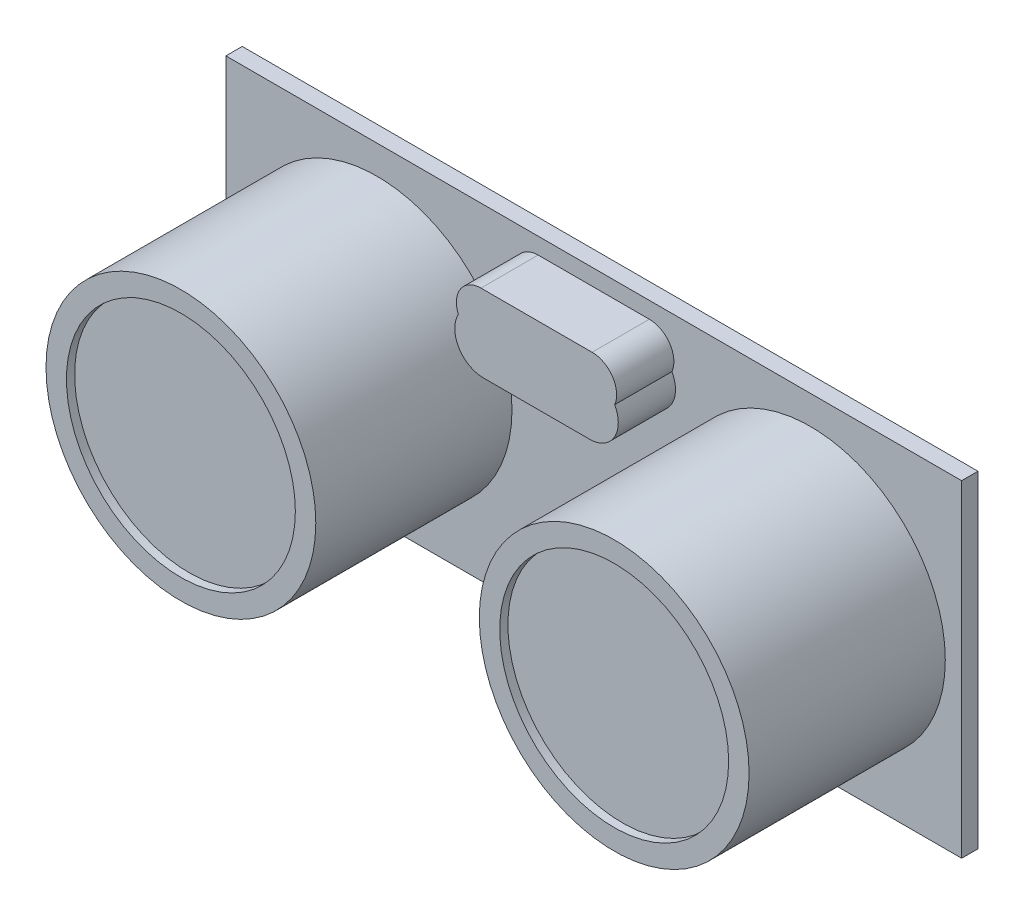
SolidWorks part; units mm, degrees
ref_plane "Plano frontal" through (0, 0, 0) normal (0, 0, 1) x (1, 0, 0)
ref_plane "Plano superior" through (0, 0, 0) normal (0, 1, 0) x (1, 0, 0)
ref_plane "Plano direito" through (0, 0, 0) normal (1, 0, 0) x (0, 0, -1)
sketch "Esboço1" plane through (0, 0, 0) normal (0, 0, 1) x (1, 0, 0)
  line L1 (0, 0) -> (45, 0)
  line L2 (0, 0) -> (0, 20)
  line L3 (0, 20) -> (45, 20)
  line L4 (45, 0) -> (45, 20)
  dimension "D1" = 45
  dimension "D2" = 20
extrude "Ressalto-extrusão1" add sketch "Esboço1" along normal blind 1
sketch "Esboço2" plane through (0, 0, 1) normal (0, 0, 1) x (1, 0, 0)
  line L0 (0, 10) -> (45, 10) construction
  line L1 (0, 20) -> (0, 0) construction
  line L2 (45, 0) -> (45, 20) construction
  line L3 (9.25, 20) -> (9.25, 0) construction
  line L4 (45, 20) -> (0, 20) construction
  line L5 (0, 0) -> (45, 0) construction
  line L6 (35.75, 20) -> (35.75, 0) construction
  circle A0 centre (9.25, 10) radius 8.25
  circle A1 centre (35.75, 10) radius 8.25
  dimension "D1" = 26.5
  dimension "D2" = 9.25
extrude "Ressalto-extrusão2" add sketch "Esboço2" along normal blind 12
sketch "Esboço3" plane through (0, 0, 13) normal (0, 0, 1) x (1, 0, 0)
  circle A0 centre (9.25, 10) radius 7
  circle A1 centre (35.75, 10) radius 7
extrude "Corte-extrusão1" cut sketch "Esboço3" against normal blind 0.5
sketch "Esboço6" plane through (0, 0, 1) normal (0, 0, 1) x (1, 0, 0)
  line L0 (22.5, 20) -> (22.5, 0) construction
  line L1 (17.5, 14.3168) -> (27.5, 14.3168)
  line L2 (17.5, 14.3168) -> (17.5, 17.8168)
  line L3 (17.5, 17.8168) -> (27.5, 17.8168)
  line L4 (27.5, 14.3168) -> (27.5, 17.8168)
  line L5 (45, 20) -> (0, 20) construction
  line L6 (0, 0) -> (45, 0) construction
  circle A2 centre (19.25, 16.0668) radius 1.75
  circle A3 centre (25.75, 16.0668) radius 1.75
  dimension "D1" = 10
  dimension "D2" = 3.5
  dimension "D3" = 5
extrude "Ressalto-extrusão5" add sketch "Esboço6" along normal blind 3.5 contours A2 | L0 L3 A2 L1 | L3 L0 L1 A3 | A3
sketch "Esboço7" plane through (0, 0, 0) normal (0, 0, -1) x (-1, 0, 0)
  line L0 (0, 0) -> (-45, 0) construction
  line L1 (-27.5, 0) -> (-17.5, 0)
  line L2 (-27.5, 0) -> (-27.5, 2)
  line L3 (-27.5, 2) -> (-17.5, 2)
  line L4 (-17.5, 0) -> (-17.5, 2)
  line L5 (-22.5, 20) -> (-22.5, 0) construction
  line L6 (-25.5, 2) -> (-25.5, 0)
  line L7 (-45, 20) -> (0, 20) construction
  line L8 (-23.5, 2) -> (-23.5, 0)
  line L9 (-21.5, 2) -> (-21.5, 0)
  line L10 (-19.5, 2) -> (-19.5, 0)
  line L11 (-25.6, 2) -> (-25.6, 0)
  line L12 (-23.6, 2) -> (-23.6, 0)
  line L13 (-21.6, 2) -> (-21.6, 0)
  line L14 (-19.6, 2) -> (-19.6, 0)
  line L15 (-27.6, -0.1) -> (-27.6, 2.1)
  line L16 (-27.6, 2.1) -> (-17.4, 2.1)
  line L17 (-17.4, -0.1) -> (-17.4, 2.1)
  line L18 (-27.6, -0.1) -> (-17.4, -0.1)
  line L19 (-25.4, 2) -> (-25.4, 0)
  line L20 (-23.4, 2) -> (-23.4, 0)
  line L21 (-21.4, 2) -> (-21.4, 0)
  line L22 (-19.4, 2) -> (-19.4, 0)
  line L23 (-27.4, 0.1) -> (-27.4, 1.9)
  line L24 (-27.4, 1.9) -> (-17.6, 1.9)
  line L25 (-17.6, 0.1) -> (-17.6, 1.9)
  line L26 (-27.4, 0.1) -> (-17.6, 0.1)
  line L28 (-25.6, 1.9) -> (-19.4, 1.9)
  line L29 (-25.6, 1.9) -> (-25.6, 0.1)
  line L30 (-25.6, 0.1) -> (-19.4, 0.1)
  line L31 (-19.4, 1.9) -> (-19.4, 0.1)
  line M23 (-45, 0) -> (0, 0)
  dimension "D1" = 5
  dimension "D2" = 10
  dimension "D3" = 2
  dimension "D4" = 2
  dimension "D5" = 2
  dimension "D6" = 2
  dimension "D7" = 2
  dimension "D10" = 0.1
  dimension "D11" = 0.1
  dimension "D8" = 0.1
  dimension "D9" = 0.1
extrude "Ressalto-extrusão6" add sketch "Esboço7" along normal blind 2 contours L23 L26 L11 L24 | L19 L26 L12 L24 | L5 L24 L20 L26 | L28 L5 L30 L13 | L21 L26 L14 L24 | L22 L26 L25 L24 | L26 L23 L24 L11 L3 L2 M23 | L19 L24 L12 L3 | L5 L3 L20 L24 | L3 L5 L28 L13 | L21 L24 L14 L3 | L26 L22 L1 L4 L3 L24 L25 | L26 L19 L12 M23 | L5 L26 L20 L1 | L30 L5 L13 M23 | L26 L21 L14 M23
sketch "Esboço9" plane through (0, 0, -2) normal (0, 0, -1) x (-1, 0, 0)
  line L0 (-17.5, 0) -> (-17.5, 2) construction
  line L1 (-27.5, 0) -> (-17.5, 0)
  line L2 (-27.5, 0) -> (-27.5, 0.1)
  line L3 (-27.5, 0.1) -> (-17.5, 0.1)
  line L4 (-17.5, 0) -> (-17.5, 0.1)
  dimension "D1" = 0.1
extrude "Corte-extrusão2" cut sketch "Esboço9" against normal blind 2
sketch "Esboço10" plane through (0, 0, -2) normal (0, 0, -1) x (-1, 0, 0)
  line L0 (-27.5, 1.05) -> (-25, 1.05) construction
  line L1 (-27.5, 0.1) -> (-27.5, 2) construction
  line L2 (-17.5, 0.1) -> (-17.5, 2) construction
  line L3 (-26.55, 2) -> (-26.55, 0.1) construction
  line L4 (-27.5, 2) -> (-25.6, 2) construction
  line L5 (-25.6, 0.1) -> (-27.5, 0.1) construction
  line L6 (-24.5, 2) -> (-24.5, 1.55) construction
  line L7 (-25.4, 2) -> (-23.6, 2) construction
  line L8 (-23.6, 0.1) -> (-25.4, 0.1) construction
  line L9 (-22.5, 2) -> (-22.5, 0.1) construction
  line L10 (-23.4, 2) -> (-21.6, 2) construction
  line L11 (-21.6, 0.1) -> (-23.4, 0.1) construction
  line L12 (-20.5, 2) -> (-20.5, 0.1) construction
  line L13 (-21.4, 2) -> (-19.6, 2) construction
  line L14 (-19.6, 0.1) -> (-21.4, 0.1) construction
  line L15 (-18.45, 2) -> (-18.45, 0.1) construction
  line L16 (-19.4, 2) -> (-17.5, 2) construction
  line L17 (-17.5, 0.1) -> (-19.4, 0.1) construction
  line L18 (-25, 0.55) -> (-24, 0.55)
  line L21 (-25, 1.55) -> (-24, 1.55)
  line L22 (-24, 0.55) -> (-24, 1.55)
  line L23 (-25, 0.55) -> (-25, 1.55)
  line L24 (-24.5, 0.55) -> (-24.5, 0.1) construction
  line L25 (-24, 1.05) -> (-17.5, 1.05) construction
  line L26 (-27.05, 0.55) -> (-26.05, 0.55)
  line L27 (-27.05, 1.55) -> (-26.05, 1.55)
  line L28 (-26.05, 0.55) -> (-26.05, 1.55)
  line L29 (-27.05, 0.55) -> (-27.05, 1.55)
  line L30 (-22.9724, 0.55) -> (-21.9724, 0.55)
  line L31 (-22.9724, 1.55) -> (-21.9724, 1.55)
  line L32 (-21.9724, 0.55) -> (-21.9724, 1.55)
  line L33 (-22.9724, 0.55) -> (-22.9724, 1.55)
  line L34 (-20.9694, 0.55) -> (-19.9694, 0.55)
  line L35 (-20.9694, 1.55) -> (-19.9694, 1.55)
  line L36 (-19.9694, 0.55) -> (-19.9694, 1.55)
  line L37 (-20.9694, 0.55) -> (-20.9694, 1.55)
  line L38 (-18.9714, 0.55) -> (-17.9714, 0.55)
  line L39 (-18.9714, 1.55) -> (-17.9714, 1.55)
  line L40 (-17.9714, 0.55) -> (-17.9714, 1.55)
  line L41 (-18.9714, 0.55) -> (-18.9714, 1.55)
  dimension "D1" = 0.5
  dimension "D2" = 0.5
  dimension "D3" = 0.5
  dimension "D4" = 1
  dimension "D5" = 1
  dimension "D6" = 1
  dimension "D7" = 1
  dimension "D8" = 1
  dimension "D9" = 1
  dimension "D10" = 1
  dimension "D11" = 1
  dimension "D12" = 1
  dimension "D13" = 1
  dimension "D14" = 0.5
  dimension "D15" = 0.5
  dimension "D16" = 0.5
  dimension "D17" = 0.5
  dimension "D18" = 0.5
extrude "Ressalto-extrusão7" add sketch "Esboço10" along normal blind 2
sketch "Esboço11" plane through (0, 0.55, 0) normal (0, -1, 0) x (1, 0, 0)
  line L0 (26.05, -4) -> (26.05, -2) construction
  line L1 (27.05, -4) -> (26.05, -4)
  line L2 (27.05, -4) -> (27.05, -3)
  line L3 (27.05, -3) -> (26.05, -3)
  line L4 (26.05, -4) -> (26.05, -3)
  line L21 (24, -4) -> (24, -2) construction
  line L22 (25, -4) -> (24, -4)
  line L23 (25, -4) -> (25, -3)
  line L24 (25, -3) -> (24, -3)
  line L25 (24, -4) -> (24, -3)
  line L26 (22.9724, -4) -> (22.9724, -2) construction
  line L27 (22.9724, -4) -> (21.9724, -4)
  line L28 (22.9724, -4) -> (22.9724, -3.0323)
  line L29 (22.9724, -3.0323) -> (21.9724, -3.0323)
  line L30 (21.9724, -4) -> (21.9724, -3.0323)
  line L31 (21.9724, -4) -> (21.9724, -2) construction
  line L32 (19.9694, -4) -> (19.9694, -2) construction
  line L33 (20.9694, -4) -> (19.9694, -4)
  line L34 (20.9694, -4) -> (20.9694, -3.0323)
  line L35 (20.9694, -3.0323) -> (19.9694, -3.0323)
  line L36 (19.9694, -4) -> (19.9694, -3.0323)
  line L37 (17.9714, -4) -> (17.9714, -2) construction
  line L38 (18.9714, -4) -> (17.9714, -4)
  line L39 (18.9714, -4) -> (18.9714, -3.0323)
  line L40 (18.9714, -3.0323) -> (17.9714, -3.0323)
  line L41 (17.9714, -4) -> (17.9714, -3.0323)
  dimension "D1" = 1
extrude "Ressalto-extrusão8" add sketch "Esboço11" along normal blind 4
sketch "Esboço4" plane through (0, 0, 1) normal (0, 0, 1) x (1, 0, 0)
  line L0 (45, 20) -> (0, 20) construction
  line L1 (19.1, 19) -> (25.9, 19)
  line L3 (19.1, 16) -> (25.9, 16)
  line L5 (22.5, 20) -> (22.5, 0) construction
  line L6 (0, 0) -> (45, 0) construction
  line L7 (17.6, 17.5) -> (27.4, 17.5) construction
  circle A0 centre (19.1, 17.5) radius 1.5
  circle A1 centre (25.9, 17.5) radius 1.5
  arc M14 (19.25, 14.3168) -> (19.25, 17.8168) centre (19.25, 16.0668) cw
  line M15 (19.25, 17.8168) -> (25.75, 17.8168)
  arc M16 (25.75, 17.8168) -> (25.75, 14.3168) centre (25.75, 16.0668) cw
  dimension "D3" = 1
extrude "Ressalto-extrusão3" add sketch "Esboço4" along normal blind 3.5 contours A0 M15 M14 | A1 L1 A0 M15 | A1 M15 M16 | A0 M14 M15 | A1 A0 L3 M15 | A1 M15 M16
